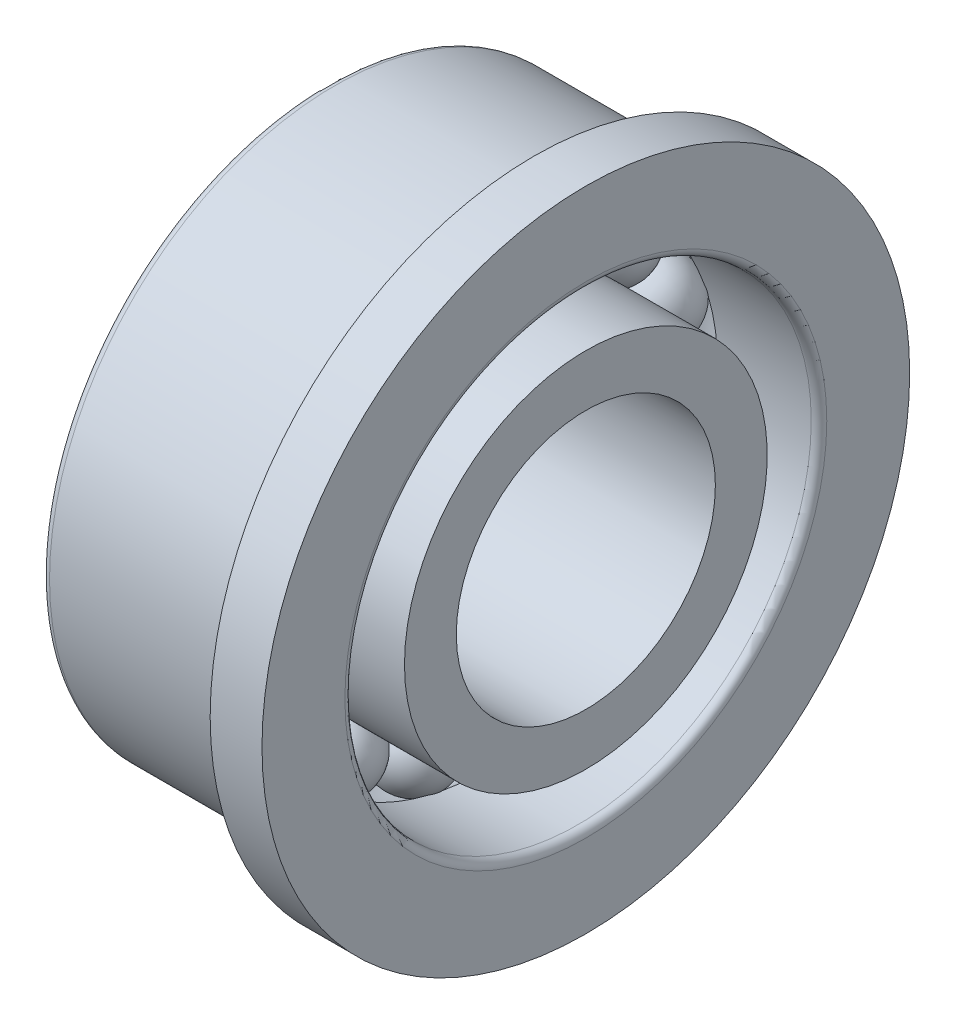
SolidWorks part; units mm, degrees
ref_plane "Front" through (0, 0, 0) normal (0, 0, 1) x (1, 0, 0)
ref_plane "Top" through (0, 0, 0) normal (0, 1, 0) x (1, 0, 0)
ref_plane "Right" through (0, 0, 0) normal (1, 0, 0) x (0, 0, -1)
sketch "Sketch1" plane through (0, 0, 0) normal (0, 0, 1) x (1, 0, 0)
  line L0 (-0.8071, 0) -> (0.9386, 0) construction
  line L1 (-0.8071, 4) -> (0.9386, 4) construction
  line L2 (-0.75, 4) -> (0.75, 4)
  arc A0 (-0.75, 4) -> (0.75, 4) centre (0, 4) ccw
  dimension "D2" = 1.5
  dimension "D1" = 4
revolve "Revolve1" add sketch "Sketch1" angle 360 about L1
sketch "Sketch2" plane through (0, 0, 0) normal (0, 0, 1) x (1, 0, 0)
  line L0 (-2.5, 3.5) -> (-0.5455, 3.5)
  line L1 (2.5, 3.5) -> (2.5, 2.5)
  line L2 (2.5, 2.5) -> (-2.5, 2.5)
  line L3 (-2.5, 2.5) -> (-2.5, 3.5)
  line L4 (-0.8417, 0) -> (1.1297, 0) construction
  line L5 (-0.8417, 4) -> (0.9121, 4) construction
  line L6 (0.5455, 3.5) -> (2.5, 3.5)
  arc A0 (-0.5455, 3.5) -> (0.5455, 3.5) centre (0, 4) ccw
  dimension "D6" = 1.48
  dimension "D1" = 5
  dimension "D2" = 4
  dimension "D3" = 5
  dimension "D4" = 2.5
  dimension "D5" = 7
revolve "Revolve2" add sketch "Sketch2" angle 360 about L4
sketch "Sketch3" plane through (0, 0, 0) normal (0, 0, 1) x (1, 0, 0)
  line L0 (-2.5, 5.5) -> (-2.5, 4.5)
  line L1 (-2.5, 4.5) -> (-0.5455, 4.5)
  line L2 (2.5, 4.5) -> (2.5, 6.25)
  line L3 (2.5, 6.25) -> (1.5, 6.25)
  line L4 (1.5, 6.25) -> (1.5, 5.5375)
  line L5 (1.4625, 5.5) -> (-2.5, 5.5)
  line L6 (-0.9997, 0) -> (1.1297, 0) construction
  line L8 (-0.9997, 4) -> (0.9355, 4) construction
  line L9 (0.5455, 4.5) -> (2.5, 4.5)
  arc A0 (0.5455, 4.5) -> (-0.5455, 4.5) centre (0, 4) ccw
  arc A1 (1.4625, 5.5) -> (1.5, 5.5375) centre (1.5, 5.5) ccw
  dimension "D8" = 1.48
  dimension "D1" = 0.075
  dimension "R" = 4
  dimension "DD" = 11
  dimension "DD1" = 12.5
  dimension "C1" = 1
  dimension "B" = 5
  dimension "D6" = 2.5
  dimension "D7" = 9
revolve "Revolve3" add sketch "Sketch3" angle 360 about L6
pattern_circular "Circular-Pattern1" count 15 over 360 about axis through (0, 0, 0) along (1, 0, 0) of "Revolve1"
fillet "Fillet1" radius 0.15 3 edges at (2.5, 0, 4.5) (-2.5, 0, 5.5) (-2.5, 0, 2.5)
equation "\"D1@Sketch1\" = ( \"DD@Sketch3\" + \"D1@Sketch2\" )  / 4"
equation "\"D2@Sketch1\" =  ( \"DD@Sketch3\" - \"D1@Sketch2\" )  / 4"
equation "\"D4@Sketch2\" = \"D3@Sketch2\" / 2"
equation "\"D5@Sketch2\" = \"D1@Sketch2\" +  ( \"DD@Sketch3\" - \"D1@Sketch2\" )  / 3"
equation "\"D2@Sketch2\" = ( \"DD@Sketch3\" + \"D1@Sketch2\" )  / 4"
equation "\"D6@Sketch2\" =  ( \"DD@Sketch3\" - \"D1@Sketch2\" )  / 4 - 0.02"
equation "\"B@Sketch3\" = \"D3@Sketch2\""
equation "\"D6@Sketch3\" = \"B@Sketch3\" / 2"
equation "\"R@Sketch3\" = ( \"DD@Sketch3\" + \"D1@Sketch2\" )  / 4"
equation "\"D7@Sketch3\" = \"DD@Sketch3\" -  ( \"DD@Sketch3\"  - \"D1@Sketch2\") / 3 "
equation "\"D8@Sketch3\" = ( \"DD@Sketch3\" - \"D1@Sketch2\" )  / 4 - 0.02"
equation "\"m@Circular-Pattern1\" = int( 3.14159265 / atn((\"D2@Sketch1\"/2) / sqr(( \"DD@Sketch3\" + \"D1@Sketch2\" )  / 4 * ( \"DD@Sketch3\" + \"D1@Sketch2\" )  / 4 - (\"D2@Sketch1\"/2) *  (\"D2@Sketch1\"/2))))-1"
equation "\"D1@Sketch3\" =  ( \"DD1@Sketch3\" - \"DD@Sketch3\" )  / 20"
